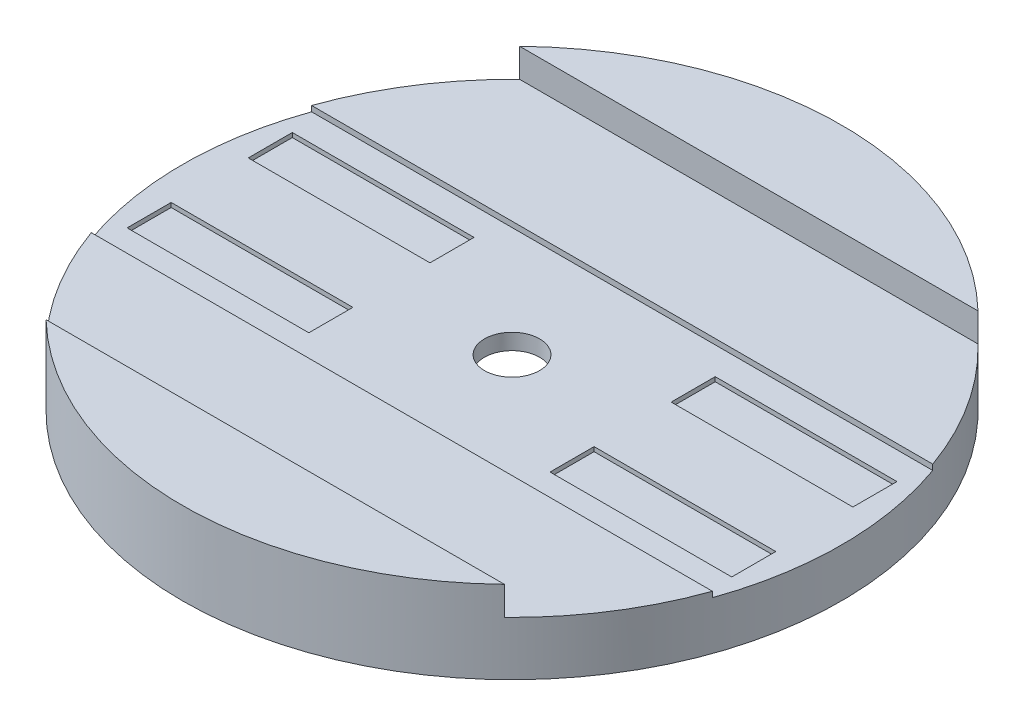
SolidWorks part; units mm, degrees
ref_plane "Front Plane" through (0, 0, 0) normal (0, 0, 1) x (1, 0, 0)
ref_plane "Top Plane" through (0, 0, 0) normal (0, 1, 0) x (1, 0, 0)
ref_plane "Right Plane" through (0, 0, 0) normal (1, 0, 0) x (0, 0, -1)
sketch "Sketch1" plane through (0, 0, 0) normal (0, 1, 0) x (1, 0, 0)
  circle A0 centre (0, 0) radius 76
  dimension "D1" = 152
extrude "Boss-Extrude1" add sketch "Sketch1" along normal blind 19.05 contours A0
sketch "Sketch2" plane through (0, 19.05, 0) normal (0, 1, 0) x (1, 0, 0)
  line L0 (-76, 0) -> (76, 0) construction
  line L1 (-58.008, 0) -> (58.008, 0) construction
  line L2 (-58.008, 54.61) -> (58.008, 54.61)
  line L3 (-58.008, -54.61) -> (58.008, -54.61)
  circle A0 centre (0, 0) radius 76 construction
  arc A1 (-58.008, 54.61) -> (-58.008, -54.61) centre (-58.008, 0) ccw
  arc A2 (58.008, -54.61) -> (58.008, 54.61) centre (58.008, 0) ccw
  point P7 (0, 0)
  dimension "D1" = 54.61
extrude "Cut-Extrude4" cut sketch "Sketch2" against normal blind 6.604
sketch "Sketch5" plane through (0, 12.446, 0) normal (0, 1, 0) x (1, 0, 0)
  line L0 (0, 6.35) -> (0, -6.35)
  circle A0 centre (0, 0) radius 6.35
  dimension "D1" = 12.7
extrude "Cut-Extrude5" cut sketch "Sketch5" against normal blind 20 contours A0
sketch "Sketch7" plane through (0, 12.446, 0) normal (0, 1, 0) x (1, 0, 0)
  line L0 (-50.1251, 42.3228) -> (-67.9029, 6.4906)
  line L1 (-67.9029, 6.4906) -> (-22.9029, 6.4906)
  line L2 (-22.9029, 6.4906) -> (-50.1251, 42.3228)
  line L3 (0, 54.61) -> (0, -54.61) construction
  line L4 (52.8559, 54.61) -> (-52.8559, 54.61) construction
  line L5 (-52.8559, -54.61) -> (52.8559, -54.61) construction
  line L6 (67.9029, 6.4906) -> (22.9029, 6.4906)
  line L7 (50.1251, 42.3228) -> (67.9029, 6.4906)
  line L8 (22.9029, 6.4906) -> (50.1251, 42.3228)
  line L9 (-76, 0) -> (76, 0) construction
  line L10 (50.1251, -42.3228) -> (67.9029, -6.4906)
  line L11 (22.9029, -6.4906) -> (50.1251, -42.3228)
  line L12 (67.9029, -6.4906) -> (22.9029, -6.4906)
  line L13 (-67.9029, -6.4906) -> (-22.9029, -6.4906)
  line L14 (-50.1251, -42.3228) -> (-67.9029, -6.4906)
  line L15 (-22.9029, -6.4906) -> (-50.1251, -42.3228)
  arc A0 (-52.8559, 54.61) -> (-52.8559, -54.61) centre (0, 0) ccw construction
  arc A1 (52.8559, -54.61) -> (52.8559, 54.61) centre (0, 0) ccw construction
  dimension "D1" = 40
  dimension "D2" = 45
  dimension "D3" = 45
extrude "Cut-Extrude6" [suppressed] cut sketch "Sketch7" against normal through all
sketch "Sketch9" [suppressed] plane through (0, 11.938, 0) normal (0, 1, 0) x (1, 0, 0)
  line L0 (-12.5, 6.4906) -> (-12.5, 42.3228)
  line L1 (-12.5, 42.3228) -> (-39.5, 42.3228)
  line L2 (-12.5, 6.4906) -> (-39.5, 42.3228)
  line L3 (0, 54.61) -> (0, -54.61) construction
  line L4 (52.8559, 54.61) -> (-52.8559, 54.61) construction
  line L5 (-52.8559, -54.61) -> (52.8559, -54.61) construction
  line L6 (-76, 0) -> (76, 0) construction
  line L7 (12.5, 6.4906) -> (39.5, 42.3228)
  line L8 (12.5, 42.3228) -> (39.5, 42.3228)
  line L9 (12.5, 6.4906) -> (12.5, 42.3228)
  line L10 (12.5, -6.4906) -> (12.5, -42.3228)
  line L11 (12.5, -42.3228) -> (39.5, -42.3228)
  line L12 (12.5, -6.4906) -> (39.5, -42.3228)
  line L13 (-12.5, -6.4906) -> (-39.5, -42.3228)
  line L14 (-12.5, -42.3228) -> (-39.5, -42.3228)
  line L15 (-12.5, -6.4906) -> (-12.5, -42.3228)
  arc A0 (-52.8559, 54.61) -> (-52.8559, -54.61) centre (0, 0) ccw construction
  arc A1 (52.8559, -54.61) -> (52.8559, 54.61) centre (0, 0) ccw construction
  dimension "D1" = 27
  dimension "D2" = 12.5
  dimension "D3" = 27
extrude "Cut-Extrude7" [suppressed] cut sketch "Sketch9" against normal through all
sketch "Sketch10" [suppressed] plane through (0, 11.938, 0) normal (0, 1, 0) x (1, 0, 0)
  line L0 (-22.9029, 6.4906) -> (-50.1251, 42.3228) construction
  line L1 (-39.5, 42.3228) -> (-12.5, 6.4906) construction
  dimension "D1" = 16.5359
sketch "Sketch11" plane through (0, 0, 0) normal (0, -1, 0) x (1, 0, 0)
sketch "Sketch13" plane through (0, 0, 0) normal (0, -1, 0) x (-1, 0, 0)
  circle A0 centre (0, 0) radius 70
  dimension "D1" = 140
extrude "Cut-Extrude9" cut sketch "Sketch13" against normal blind 7.5
sketch "Sketch15" plane through (0, 12.446, 0) normal (0, 1, 0) x (1, 0, 0)
  line L0 (76, 0) -> (-76, 0) construction
  line L1 (76, -25.4) -> (-76, -25.4)
  line L2 (76, 25.4) -> (-76, 25.4)
  arc A0 (-52.8559, 54.61) -> (-52.8559, -54.61) centre (0, 0) ccw construction
  arc A1 (76, -25.4) -> (76, 25.4) centre (76, 0) ccw
  arc A2 (-76, 25.4) -> (-76, -25.4) centre (-76, 0) ccw
  point P6 (0, 0)
  dimension "D1" = 25.4
extrude "Cut-Extrude11" cut sketch "Sketch15" against normal blind 1.27
sketch "Sketch16" plane through (0, 11.176, 0) normal (0, 1, 0) x (1, 0, 0)
  line L1 (71.6299, 25.4) -> (-71.6299, 25.4) construction
  line L4 (-69.723, -8.89) -> (-27.813, -8.89)
  line L5 (-69.723, 19.05) -> (-27.813, 19.05)
  line L6 (-69.723, 19.05) -> (-69.723, 8.89)
  line L7 (-69.723, 8.89) -> (-27.813, 8.89)
  line L8 (-27.813, 19.05) -> (-27.813, 8.89)
  line L9 (-27.813, -19.05) -> (-27.813, -8.89)
  line L10 (-69.723, -19.05) -> (-27.813, -19.05)
  line L11 (-69.723, -19.05) -> (-69.723, -8.89)
  line L12 (69.723, -19.05) -> (69.723, -8.89)
  line L13 (69.723, -19.05) -> (27.813, -19.05)
  line L14 (27.813, -19.05) -> (27.813, -8.89)
  line L15 (69.723, -8.89) -> (27.813, -8.89)
  line L16 (69.723, 8.89) -> (27.813, 8.89)
  line L17 (27.813, 19.05) -> (27.813, 8.89)
  line L18 (69.723, 19.05) -> (27.813, 19.05)
  line L19 (69.723, 19.05) -> (69.723, 8.89)
  dimension "D1" = 6.35
  dimension "D2" = 41.91
  dimension "D3" = 10.16
  dimension "D4" = 55.626
extrude "Cut-Extrude12" cut sketch "Sketch16" against normal blind 1.016
